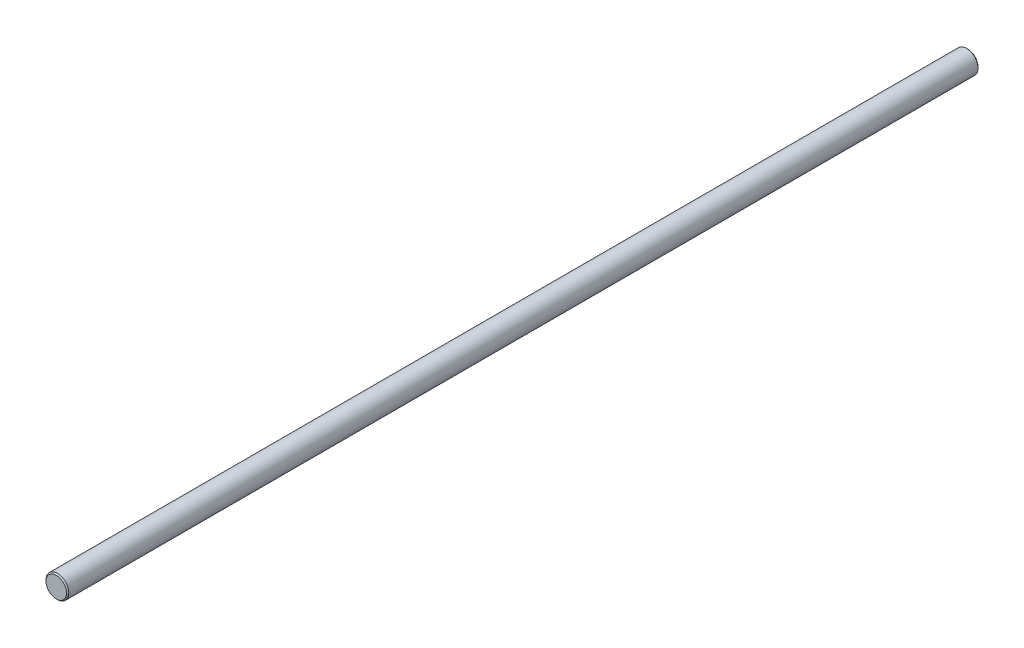
SolidWorks part; units mm, degrees
ref_plane "Plano frontal" through (0, 0, 0) normal (0, 0, 1) x (1, 0, 0)
ref_plane "Plano superior" through (0, 0, 0) normal (0, 1, 0) x (1, 0, 0)
ref_plane "Plano direito" through (0, 0, 0) normal (1, 0, 0) x (0, 0, -1)
sketch "Esboço1" plane through (0, 0, 0) normal (0, 0, 1) x (1, 0, 0)
  circle A0 centre (0, 0) radius 5
  dimension "D1" = 10
extrude "Ressalto-extrusão1" add sketch "Esboço1" along normal blind 400
chamfer "Chanfro1" distance 0.5 angle 45 2 edges at (5, 0, 400) (5, 0, 0)
